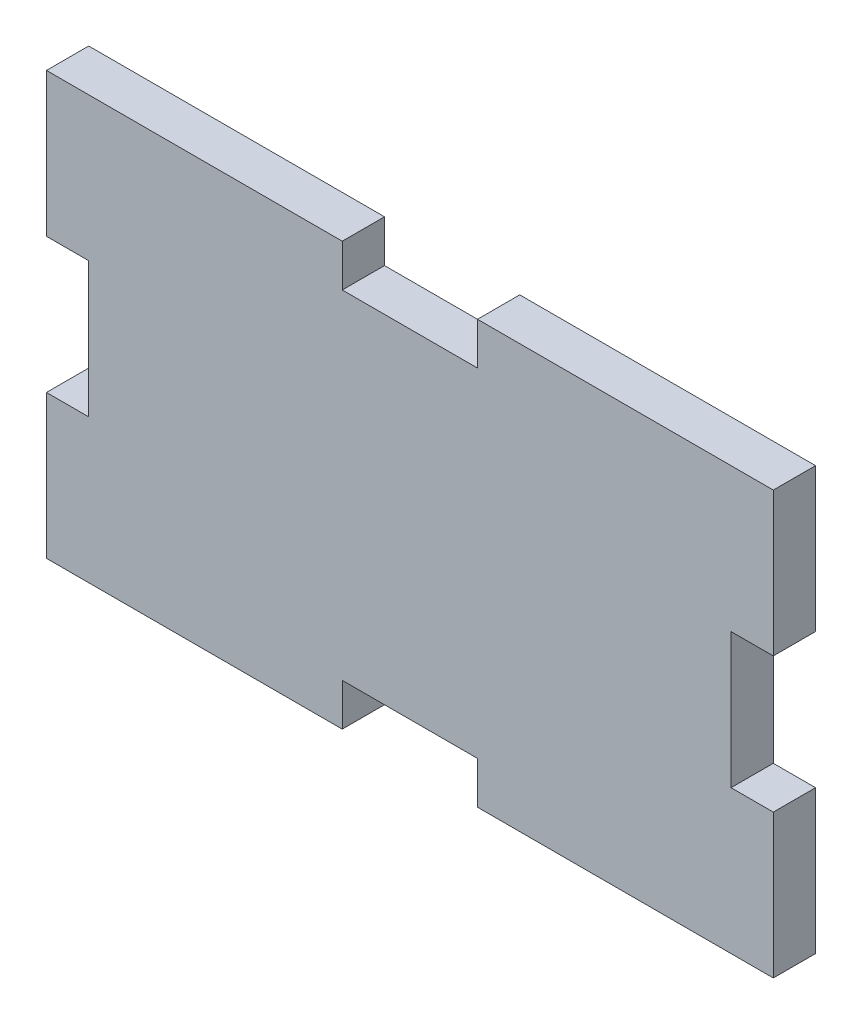
SolidWorks part; units mm, degrees
ref_plane "Front Plane" through (0, 0, 0) normal (0, 0, 1) x (1, 0, 0)
ref_plane "Top Plane" through (0, 0, 0) normal (0, 1, 0) x (1, 0, 0)
ref_plane "Right Plane" through (0, 0, 0) normal (1, 0, 0) x (0, 0, -1)
sketch "Sketch1" plane through (0, 0, 0) normal (0, 0, 1) x (1, 0, 0)
  line L0 (0, 39.1319) -> (0, 20) construction
  line L1 (-43, 25) -> (-8, 25)
  line L2 (-43, 25) -> (-43, 8)
  line L3 (-43, -25) -> (-8, -25)
  line L4 (43, 25) -> (43, 8)
  line L5 (-43, 25) -> (43, -25) construction
  line L6 (-43, -25) -> (43, 25) construction
  line L7 (-51.9064, 0) -> (-38, 0) construction
  line L8 (-8, 25) -> (-8, 20)
  line L9 (-8, 20) -> (8, 20)
  line L10 (8, 20) -> (8, 25)
  line L11 (43, 8) -> (38, 8)
  line L12 (38, 8) -> (38, -8)
  line L13 (38, -8) -> (43, -8)
  line L14 (-43, 8) -> (-38, 8)
  line L15 (-38, 8) -> (-38, -8)
  line L16 (-38, -8) -> (-43, -8)
  line L17 (-8, -25) -> (-8, -20)
  line L18 (-8, -20) -> (8, -20)
  line L19 (8, -20) -> (8, -25)
  line L20 (-43, -8) -> (-43, -25)
  line L21 (-38, 0) -> (38, 0) construction
  line L22 (43, -8) -> (43, -25)
  line L23 (38, 0) -> (67.7532, 0) construction
  line L24 (8, -25) -> (43, -25)
  line L25 (0, -20) -> (0, -39.7787) construction
  line L26 (8, 25) -> (43, 25)
  line L27 (0, 20) -> (0, -20) construction
  point P0 (0, 0)
  dimension "D1" = 86
  dimension "D2" = 50
  dimension "D3" = 5
  dimension "D4" = 5
  dimension "D5" = 16
  dimension "D6" = 16
  dimension "D7" = 16
  dimension "D8" = 5
  dimension "D9" = 5
  dimension "D10" = 16
extrude "Boss-Extrude1" add sketch "Sketch1" along normal blind 5
